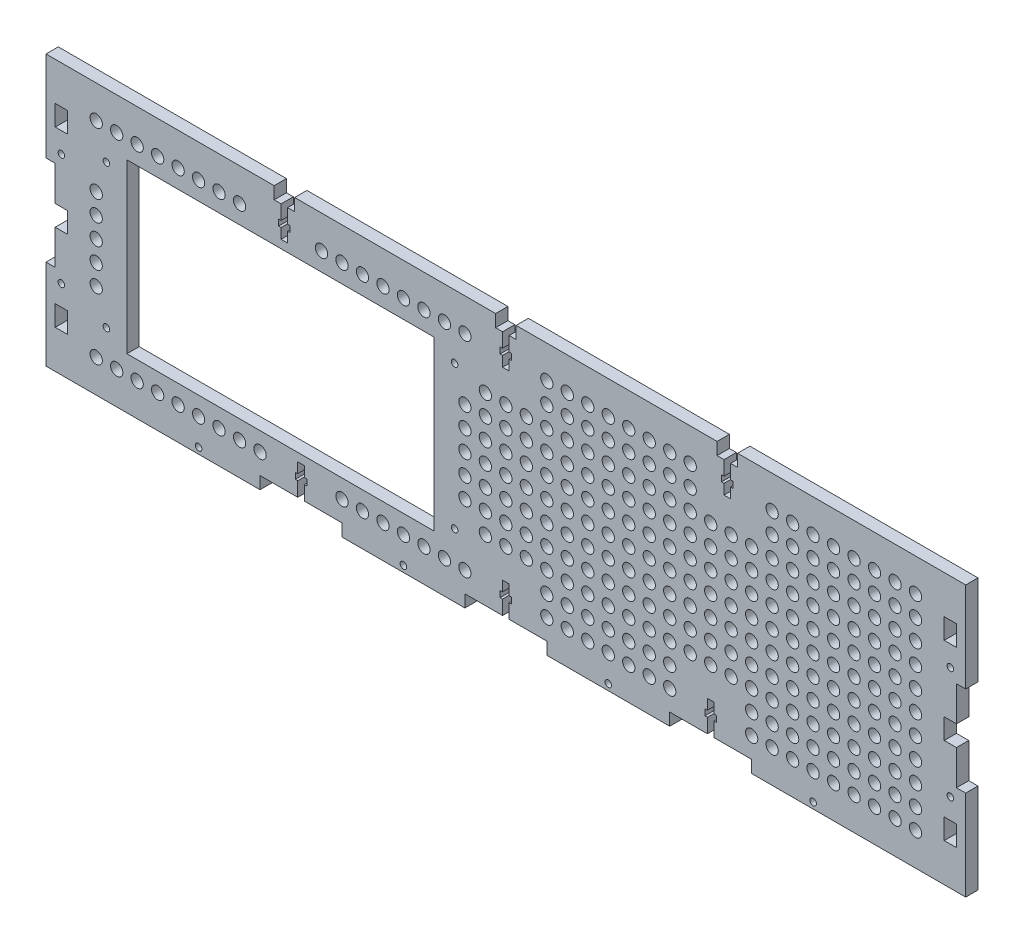
SolidWorks part; units mm, degrees
ref_plane "Front Plane" through (0, 0, 0) normal (0, 0, 1) x (1, 0, 0)
ref_plane "Top Plane" through (0, 0, 0) normal (0, 1, 0) x (1, 0, 0)
ref_plane "Right Plane" through (0, 0, 0) normal (1, 0, 0) x (0, 0, -1)
sketch "Sketch1" plane through (0, 0, 0) normal (0, 0, 1) x (1, 0, 0)
  line L1 (-220, -66) -> (220, -66)
  line L2 (-220, -66) -> (-220, 66)
  line L3 (-220, 66) -> (220, 66)
  line L4 (220, -66) -> (220, 66)
  line L5 (-220, -66) -> (220, 66) construction
  line L6 (-220, 66) -> (220, -66) construction
  point P0 (0, 0)
  dimension "D1" = 440
  dimension "D2" = 132
extrude "Boss-Extrude1" add sketch "Sketch1" along normal blind 6
sketch "Sketch2" plane through (0, 0, 0) normal (0, 0, -1) x (-1, 0, 0)
  line L0 (220, 47.3321) -> (220, 37.3321) construction
  line L1 (220, 37.3321) -> (214, 37.3321) construction
  line L2 (214, 37.3321) -> (214, 47.3321) construction
  line L3 (214, 47.3321) -> (220, 47.3321) construction
  line L12 (220, -37.3321) -> (220, -47.3321) construction
  line L13 (220, -47.3321) -> (214, -47.3321) construction
  line L14 (214, -47.3321) -> (214, -37.3321) construction
  line L15 (214, -37.3321) -> (220, -37.3321) construction
  line L16 (220, 47.3321) -> (220, 37.3321)
  line L17 (220, 37.3321) -> (214, 37.3321)
  line L18 (214, 37.3321) -> (214, 47.3321)
  line L19 (214, 47.3321) -> (220, 47.3321)
  line L20 (220, -37.3321) -> (220, -47.3321)
  line L21 (220, -47.3321) -> (214, -47.3321)
  line L22 (214, -47.3321) -> (214, -37.3321)
  line L23 (214, -37.3321) -> (220, -37.3321)
  line L24 (-214, -37.3321) -> (-214, -47.3321) construction
  line L25 (-214, -47.3321) -> (-220, -47.3321) construction
  line L26 (-220, -47.3321) -> (-220, -37.3321) construction
  line L27 (-220, -37.3321) -> (-214, -37.3321) construction
  line L28 (-214, 47.3321) -> (-214, 37.3321) construction
  line L29 (-214, 37.3321) -> (-220, 37.3321) construction
  line L30 (-220, 37.3321) -> (-220, 47.3321) construction
  line L31 (-220, 47.3321) -> (-214, 47.3321) construction
  line L32 (-214, -37.3321) -> (-214, -47.3321)
  line L33 (-214, -47.3321) -> (-220, -47.3321)
  line L34 (-220, -47.3321) -> (-220, -37.3321)
  line L35 (-220, -37.3321) -> (-214, -37.3321)
  line L36 (-214, 47.3321) -> (-214, 37.3321)
  line L37 (-214, 37.3321) -> (-220, 37.3321)
  line L38 (-220, 37.3321) -> (-220, 47.3321)
  line L39 (-220, 47.3321) -> (-214, 47.3321)
  line L44 (220, -5) -> (220, 5)
  line L45 (214, -5) -> (220, -5)
  line L46 (214, 5) -> (214, -5)
  line L47 (220, 5) -> (214, 5)
  line L48 (220, -5) -> (220, 5)
  line L49 (214, -5) -> (220, -5)
  line L50 (214, 5) -> (214, -5)
  line L51 (220, 5) -> (214, 5)
  line L52 (-214, -5) -> (-214, 5)
  line L53 (-220, -5) -> (-214, -5)
  line L54 (-220, 5) -> (-220, -5)
  line L55 (-214, 5) -> (-220, 5)
  line L56 (-214, -5) -> (-214, 5)
  line L57 (-220, -5) -> (-214, -5)
  line L58 (-220, 5) -> (-220, -5)
  line L59 (-214, 5) -> (-220, 5)
  circle A0 centre (217, 27.3321) radius 1.6 construction
  circle A1 centre (217, -27.3321) radius 1.6 construction
  circle A2 centre (-217, 27.3321) radius 1.6 construction
  circle A3 centre (-217, -27.3321) radius 1.6 construction
  circle A4 centre (217, 27.3321) radius 1.6
  circle A5 centre (217, -27.3321) radius 1.6
  circle A6 centre (-217, 27.3321) radius 1.6
  circle A7 centre (-217, -27.3321) radius 1.6
  dimension "D2" = 0
  dimension "D3" = 0
extrude "Cut-Extrude1" cut sketch "Sketch2" against normal up to next
sketch "Sketch3" plane through (0, 0, 0) normal (0, 0, -1) x (-1, 0, 0)
  circle A0 centre (-150, -63) radius 1.6 construction
  circle A1 centre (-50, -63) radius 1.6 construction
  circle A2 centre (50, -63) radius 1.6 construction
  circle A3 centre (150, -63) radius 1.6 construction
  circle A4 centre (-150, -63) radius 1.6
  circle A5 centre (-50, -63) radius 1.6
  circle A6 centre (50, -63) radius 1.6
  circle A7 centre (150, -63) radius 1.6
extrude "Cut-Extrude2" cut sketch "Sketch3" against normal up to next
sketch "Sketch4" plane through (0, 0, 0) normal (0, 0, -1) x (-1, 0, 0)
  line L0 (80, -66) -> (120, -66) construction
  line L1 (120, -66) -> (120, -60) construction
  line L2 (120, -60) -> (80, -60) construction
  line L3 (80, -60) -> (80, -66) construction
  line L4 (-20, -66) -> (20, -66) construction
  line L5 (20, -66) -> (20, -60) construction
  line L6 (20, -60) -> (-20, -60) construction
  line L7 (-20, -60) -> (-20, -66) construction
  line L8 (-120, -66) -> (-80, -66) construction
  line L9 (-80, -66) -> (-80, -60) construction
  line L10 (-80, -60) -> (-120, -60) construction
  line L11 (-120, -60) -> (-120, -66) construction
  line L12 (80, -66) -> (120, -66)
  line L13 (120, -66) -> (120, -60)
  line L14 (120, -60) -> (80, -60)
  line L15 (80, -60) -> (80, -66)
  line L16 (-20, -66) -> (20, -66)
  line L17 (20, -66) -> (20, -60)
  line L18 (20, -60) -> (-20, -60)
  line L19 (-20, -60) -> (-20, -66)
  line L20 (-120, -66) -> (-80, -66)
  line L21 (-80, -66) -> (-80, -60)
  line L22 (-80, -60) -> (-120, -60)
  line L23 (-120, -60) -> (-120, -66)
extrude "Cut-Extrude3" cut sketch "Sketch4" against normal up to next
sketch "Sketch5" plane through (0, 66, 0) normal (0, 1, 0) x (1, 0, 0)
  line L0 (220, 0) -> (-220, 0) construction
  line L1 (-113.125, -6) -> (-103.125, -6)
  line L2 (-113.125, -6) -> (-113.125, 0)
  line L3 (-113.125, 0) -> (-103.125, 0)
  line L4 (-103.125, -6) -> (-103.125, 0)
  line L5 (-113.125, -6) -> (-103.125, 0) construction
  line L6 (-113.125, 0) -> (-103.125, -6) construction
  line L7 (-103.125, -6) -> (-103.125, 0) construction
  line L8 (5, -6) -> (5, 0) construction
  line L9 (-5, -6) -> (5, -6)
  line L10 (-5, -6) -> (-5, 0)
  line L11 (-5, 0) -> (5, 0)
  line L12 (5, -6) -> (5, 0)
  line L13 (-5, -6) -> (5, 0) construction
  line L14 (-5, 0) -> (5, -6) construction
  line L15 (113.125, -6) -> (113.125, 0) construction
  line L16 (103.125, -6) -> (113.125, -6)
  line L17 (103.125, -6) -> (103.125, 0)
  line L18 (103.125, 0) -> (113.125, 0)
  line L19 (113.125, -6) -> (113.125, 0)
  line L20 (103.125, -6) -> (113.125, 0) construction
  line L21 (103.125, 0) -> (113.125, -6) construction
  point P0 (-108.125, -3)
  point P10 (0, -3)
  point P18 (108.125, -3)
extrude "Cut-Extrude4" cut sketch "Sketch5" against normal blind 6
sketch "Sketch6" plane through (0, 0, 0) normal (0, 0, -1) x (-1, 0, 0)
  line L0 (-108.125, 60) -> (-108.125, 45) construction
  line L1 (-113.125, 60) -> (-103.125, 60) construction
  line L2 (-109.725, 60) -> (-109.725, 53)
  line L3 (-106.525, 60) -> (-106.525, 53)
  line L4 (-109.725, 60) -> (-106.525, 60)
  line L5 (-109.725, 45) -> (-106.525, 45)
  line L6 (-106.525, 50) -> (-105.325, 50)
  line L7 (-110.925, 53) -> (-109.725, 53)
  line L8 (-110.925, 53) -> (-110.925, 50)
  line L9 (-110.925, 50) -> (-109.725, 50)
  line L10 (-105.325, 53) -> (-105.325, 50)
  line L11 (-110.925, 53) -> (-105.325, 50) construction
  line L12 (-110.925, 50) -> (-105.325, 53) construction
  line L13 (-106.525, 50) -> (-106.525, 45)
  line L14 (-106.525, 60) -> (-106.525, 45) construction
  line L15 (-109.725, 50) -> (-109.725, 45)
  line L16 (-109.725, 60) -> (-109.725, 45) construction
  line L17 (-106.525, 53) -> (-105.325, 53)
  line L18 (-1.595, 60) -> (-1.595, 53)
  line L19 (1.605, 60) -> (1.605, 53)
  line L20 (-1.595, 60) -> (1.605, 60)
  line L21 (-1.595, 45) -> (1.605, 45)
  line L22 (1.605, 50) -> (2.805, 50)
  line L23 (-2.795, 53) -> (-1.595, 53)
  line L24 (-2.795, 53) -> (-2.795, 50)
  line L25 (-2.795, 50) -> (-1.595, 50)
  line L26 (2.805, 53) -> (2.805, 50)
  line L27 (1.605, 50) -> (1.605, 45)
  line L28 (-1.595, 50) -> (-1.595, 45)
  line L29 (1.605, 53) -> (2.805, 53)
  line L30 (0.005, 60) -> (0.005, 45) construction
  line L31 (-2.795, 53) -> (2.805, 50) construction
  line L32 (-2.795, 50) -> (2.805, 53) construction
  line L33 (106.535, 60) -> (106.535, 53)
  line L34 (109.735, 60) -> (109.735, 53)
  line L35 (106.535, 60) -> (109.735, 60)
  line L36 (106.535, 45) -> (109.735, 45)
  line L37 (109.735, 50) -> (110.935, 50)
  line L38 (105.335, 53) -> (106.535, 53)
  line L39 (105.335, 53) -> (105.335, 50)
  line L40 (105.335, 50) -> (106.535, 50)
  line L41 (110.935, 53) -> (110.935, 50)
  line L42 (109.735, 50) -> (109.735, 45)
  line L43 (106.535, 50) -> (106.535, 45)
  line L44 (109.735, 53) -> (110.935, 53)
  line L45 (108.135, 60) -> (108.135, 45) construction
  line L46 (105.335, 53) -> (110.935, 50) construction
  line L47 (105.335, 50) -> (110.935, 53) construction
  line L48 (-100, -60) -> (-100, -45) construction
  line L49 (-80, -60) -> (-120, -60) construction
  line L50 (-98.4, -60) -> (-98.4, -53)
  line L51 (-101.6, -60) -> (-101.6, -53)
  line L52 (-98.4, -60) -> (-101.6, -60)
  line L53 (-98.4, -45) -> (-101.6, -45)
  line L54 (-98.4, -53) -> (-97.2, -53)
  line L55 (-102.8, -50) -> (-101.6, -50)
  line L56 (-102.8, -50) -> (-102.8, -53)
  line L57 (-102.8, -53) -> (-101.6, -53)
  line L58 (-97.2, -50) -> (-97.2, -53)
  line L59 (-102.8, -50) -> (-97.2, -53) construction
  line L60 (-102.8, -53) -> (-97.2, -50) construction
  line L61 (-98.4, -50) -> (-98.4, -45)
  line L62 (-98.4, -60) -> (-98.4, -45) construction
  line L63 (-98.4, -50) -> (-97.2, -50)
  line L64 (-101.6, -50) -> (-101.6, -45)
  line L65 (-101.6, -60) -> (-101.6, -45) construction
  line L66 (1.6, -60) -> (1.6, -53)
  line L67 (1.6, -60) -> (-1.6, -60)
  line L68 (-1.6, -60) -> (-1.6, -53)
  line L69 (-2.8, -53) -> (-1.6, -53)
  line L70 (-2.8, -50) -> (-2.8, -53)
  line L71 (-2.8, -50) -> (-1.6, -50)
  line L72 (-1.6, -50) -> (-1.6, -45)
  line L73 (1.6, -45) -> (-1.6, -45)
  line L74 (1.6, -50) -> (1.6, -45)
  line L75 (1.6, -50) -> (2.8, -50)
  line L76 (2.8, -50) -> (2.8, -53)
  line L77 (1.6, -53) -> (2.8, -53)
  line L78 (101.6, -60) -> (101.6, -53)
  line L79 (101.6, -60) -> (98.4, -60)
  line L80 (98.4, -60) -> (98.4, -53)
  line L81 (97.2, -53) -> (98.4, -53)
  line L82 (97.2, -50) -> (97.2, -53)
  line L83 (97.2, -50) -> (98.4, -50)
  line L84 (98.4, -50) -> (98.4, -45)
  line L85 (101.6, -45) -> (98.4, -45)
  line L86 (101.6, -50) -> (101.6, -45)
  line L87 (101.6, -50) -> (102.8, -50)
  line L88 (102.8, -50) -> (102.8, -53)
  line L89 (101.6, -53) -> (102.8, -53)
  point P8 (-108.125, 51.5)
  point P25 (0.005, 51.5)
  point P40 (108.135, 51.5)
  point P55 (-100, -51.5)
  dimension "D1" = 15
  dimension "D4" = 5.6
  dimension "D5" = 3
  dimension "D6" = 7
  dimension "D8" = 15
  dimension "D11" = 7
  dimension "D12" = 3
  dimension "D13" = 5.6
  dimension "D2" = 1.6
  dimension "D3" = 1.6
  dimension "D9" = 1.6
  dimension "D10" = 1.6
  dimension "D7" = 3
  dimension "D14" = 3
extrude "Cut-Extrude5" cut sketch "Sketch6" against normal up to next
sketch "Sketch7" plane through (0, 0, 0) normal (0, 0, -1) x (-1, 0, 0)
  line L0 (0, 0) -> (220, 0) construction
  line L1 (220, 37.3321) -> (220, 5) construction
  line L2 (113.125, 66) -> (220, 66) construction
  line L3 (35, -41) -> (185, -41)
  line L4 (35, -41) -> (35, 41)
  line L5 (35, 41) -> (185, 41)
  line L6 (185, -41) -> (185, 41)
  line L7 (35, -41) -> (185, 41) construction
  line L8 (35, 41) -> (185, -41) construction
  line L9 (25, 35) -> (25, -35) construction
  line L10 (25, 35) -> (195, 35) construction
  line L11 (25, -35) -> (35, -35) construction
  line L12 (195, -35) -> (185, -35) construction
  circle A0 centre (25, 35) radius 1.6
  circle A1 centre (25, -35) radius 1.6
  circle A2 centre (195, 35) radius 1.6
  circle A3 centre (195, -35) radius 1.6
  point P3 (110, 0)
  point P4 (110, 0)
  point P21 (110, 35)
  point P22 (25, 0)
  dimension "D5" = 3.2
  dimension "D1" = 25
  dimension "D2" = 150
  dimension "D3" = 10
  dimension "D4" = 70
extrude "Cut-Extrude6" cut sketch "Sketch7" against normal through all
sketch "Sketch8" plane through (0, 0, 0) normal (0, 0, -1) x (-1, 0, 0)
  line L10 (-200, 50) -> (-220, 50) construction
  line L13 (-220, 22) -> (-220, 66) construction
  line L16 (200, 50) -> (220, 50) construction
  line L19 (220, 22) -> (220, 66) construction
  line L22 (-200, 50) -> (-200, 66) construction
  line L25 (-220, 66) -> (-113.125, 66) construction
  line L28 (-200, -50) -> (-200, -66) construction
  line L31 (-120, -66) -> (-220, -66) construction
  circle A128 centre (-200, 50) radius 3
  circle A129 centre (-190, 50) radius 3
  circle A130 centre (-180, 50) radius 3
  circle A131 centre (-170, 50) radius 3
  circle A132 centre (-160, 50) radius 3
  circle A133 centre (-150, 50) radius 3
  circle A134 centre (-140, 50) radius 3
  circle A135 centre (-130, 50) radius 3
  circle A139 centre (-90, 50) radius 3
  circle A140 centre (-80, 50) radius 3
  circle A141 centre (-70, 50) radius 3
  circle A142 centre (-60, 50) radius 3
  circle A143 centre (-50, 50) radius 3
  circle A144 centre (-40, 50) radius 3
  circle A145 centre (-30, 50) radius 3
  circle A146 centre (-20, 50) radius 3
  circle A150 centre (20, 50) radius 3
  circle A151 centre (30, 50) radius 3
  circle A152 centre (40, 50) radius 3
  circle A153 centre (50, 50) radius 3
  circle A154 centre (60, 50) radius 3
  circle A155 centre (70, 50) radius 3
  circle A156 centre (80, 50) radius 3
  circle A157 centre (90, 50) radius 3
  circle A161 centre (130, 50) radius 3
  circle A162 centre (140, 50) radius 3
  circle A163 centre (150, 50) radius 3
  circle A164 centre (160, 50) radius 3
  circle A165 centre (170, 50) radius 3
  circle A166 centre (180, 50) radius 3
  circle A167 centre (190, 50) radius 3
  circle A168 centre (200, 50) radius 3
  circle A169 centre (-190, 40) radius 3
  circle A170 centre (-180, 40) radius 3
  circle A171 centre (-170, 40) radius 3
  circle A172 centre (-160, 40) radius 3
  circle A173 centre (-150, 40) radius 3
  circle A174 centre (-140, 40) radius 3
  circle A175 centre (-130, 40) radius 3
  circle A179 centre (-90, 40) radius 3
  circle A180 centre (-80, 40) radius 3
  circle A181 centre (-70, 40) radius 3
  circle A182 centre (-60, 40) radius 3
  circle A183 centre (-50, 40) radius 3
  circle A184 centre (-40, 40) radius 3
  circle A185 centre (-30, 40) radius 3
  circle A186 centre (-20, 40) radius 3
  circle A209 centre (-190, 30) radius 3
  circle A210 centre (-180, 30) radius 3
  circle A211 centre (-170, 30) radius 3
  circle A212 centre (-160, 30) radius 3
  circle A213 centre (-150, 30) radius 3
  circle A214 centre (-140, 30) radius 3
  circle A215 centre (-130, 30) radius 3
  circle A216 centre (-120, 30) radius 3
  circle A217 centre (-110, 30) radius 3
  circle A218 centre (-100, 30) radius 3
  circle A219 centre (-90, 30) radius 3
  circle A220 centre (-80, 30) radius 3
  circle A221 centre (-70, 30) radius 3
  circle A222 centre (-60, 30) radius 3
  circle A223 centre (-50, 30) radius 3
  circle A224 centre (-40, 30) radius 3
  circle A225 centre (-30, 30) radius 3
  circle A226 centre (-20, 30) radius 3
  circle A227 centre (-10, 30) radius 3
  circle A228 centre (0, 30) radius 3
  circle A229 centre (10, 30) radius 3
  circle A249 centre (-190, 20) radius 3
  circle A250 centre (-180, 20) radius 3
  circle A251 centre (-170, 20) radius 3
  circle A252 centre (-160, 20) radius 3
  circle A253 centre (-150, 20) radius 3
  circle A254 centre (-140, 20) radius 3
  circle A255 centre (-130, 20) radius 3
  circle A256 centre (-120, 20) radius 3
  circle A257 centre (-110, 20) radius 3
  circle A258 centre (-100, 20) radius 3
  circle A259 centre (-90, 20) radius 3
  circle A260 centre (-80, 20) radius 3
  circle A261 centre (-70, 20) radius 3
  circle A262 centre (-60, 20) radius 3
  circle A263 centre (-50, 20) radius 3
  circle A264 centre (-40, 20) radius 3
  circle A265 centre (-30, 20) radius 3
  circle A266 centre (-20, 20) radius 3
  circle A267 centre (-10, 20) radius 3
  circle A268 centre (0, 20) radius 3
  circle A269 centre (10, 20) radius 3
  circle A270 centre (20, 20) radius 3
  circle A288 centre (200, 20) radius 3
  circle A289 centre (-190, 10) radius 3
  circle A290 centre (-180, 10) radius 3
  circle A291 centre (-170, 10) radius 3
  circle A292 centre (-160, 10) radius 3
  circle A293 centre (-150, 10) radius 3
  circle A294 centre (-140, 10) radius 3
  circle A295 centre (-130, 10) radius 3
  circle A296 centre (-120, 10) radius 3
  circle A297 centre (-110, 10) radius 3
  circle A298 centre (-100, 10) radius 3
  circle A299 centre (-90, 10) radius 3
  circle A300 centre (-80, 10) radius 3
  circle A301 centre (-70, 10) radius 3
  circle A302 centre (-60, 10) radius 3
  circle A303 centre (-50, 10) radius 3
  circle A304 centre (-40, 10) radius 3
  circle A305 centre (-30, 10) radius 3
  circle A306 centre (-20, 10) radius 3
  circle A307 centre (-10, 10) radius 3
  circle A308 centre (0, 10) radius 3
  circle A309 centre (10, 10) radius 3
  circle A310 centre (20, 10) radius 3
  circle A328 centre (200, 10) radius 3
  circle A329 centre (-190, 0) radius 3
  circle A330 centre (-180, 0) radius 3
  circle A331 centre (-170, 0) radius 3
  circle A332 centre (-160, 0) radius 3
  circle A333 centre (-150, 0) radius 3
  circle A334 centre (-140, 0) radius 3
  circle A335 centre (-130, 0) radius 3
  circle A336 centre (-120, 0) radius 3
  circle A337 centre (-110, 0) radius 3
  circle A338 centre (-100, 0) radius 3
  circle A339 centre (-90, 0) radius 3
  circle A340 centre (-80, 0) radius 3
  circle A341 centre (-70, 0) radius 3
  circle A342 centre (-60, 0) radius 3
  circle A343 centre (-50, 0) radius 3
  circle A344 centre (-40, 0) radius 3
  circle A345 centre (-30, 0) radius 3
  circle A346 centre (-20, 0) radius 3
  circle A347 centre (-10, 0) radius 3
  circle A348 centre (0, 0) radius 3
  circle A349 centre (10, 0) radius 3
  circle A350 centre (20, 0) radius 3
  circle A368 centre (200, 0) radius 3
  circle A369 centre (-190, -10) radius 3
  circle A370 centre (-180, -10) radius 3
  circle A371 centre (-170, -10) radius 3
  circle A372 centre (-160, -10) radius 3
  circle A373 centre (-150, -10) radius 3
  circle A374 centre (-140, -10) radius 3
  circle A375 centre (-130, -10) radius 3
  circle A376 centre (-120, -10) radius 3
  circle A377 centre (-110, -10) radius 3
  circle A378 centre (-100, -10) radius 3
  circle A379 centre (-90, -10) radius 3
  circle A380 centre (-80, -10) radius 3
  circle A381 centre (-70, -10) radius 3
  circle A382 centre (-60, -10) radius 3
  circle A383 centre (-50, -10) radius 3
  circle A384 centre (-40, -10) radius 3
  circle A385 centre (-30, -10) radius 3
  circle A386 centre (-20, -10) radius 3
  circle A387 centre (-10, -10) radius 3
  circle A388 centre (0, -10) radius 3
  circle A389 centre (10, -10) radius 3
  circle A390 centre (20, -10) radius 3
  circle A408 centre (200, -10) radius 3
  circle A409 centre (-190, -20) radius 3
  circle A410 centre (-180, -20) radius 3
  circle A411 centre (-170, -20) radius 3
  circle A412 centre (-160, -20) radius 3
  circle A413 centre (-150, -20) radius 3
  circle A414 centre (-140, -20) radius 3
  circle A415 centre (-130, -20) radius 3
  circle A416 centre (-120, -20) radius 3
  circle A417 centre (-110, -20) radius 3
  circle A418 centre (-100, -20) radius 3
  circle A419 centre (-90, -20) radius 3
  circle A420 centre (-80, -20) radius 3
  circle A421 centre (-70, -20) radius 3
  circle A422 centre (-60, -20) radius 3
  circle A423 centre (-50, -20) radius 3
  circle A424 centre (-40, -20) radius 3
  circle A425 centre (-30, -20) radius 3
  circle A426 centre (-20, -20) radius 3
  circle A427 centre (-10, -20) radius 3
  circle A428 centre (0, -20) radius 3
  circle A429 centre (10, -20) radius 3
  circle A430 centre (20, -20) radius 3
  circle A448 centre (200, -20) radius 3
  circle A449 centre (-190, -30) radius 3
  circle A450 centre (-180, -30) radius 3
  circle A451 centre (-170, -30) radius 3
  circle A452 centre (-160, -30) radius 3
  circle A453 centre (-150, -30) radius 3
  circle A454 centre (-140, -30) radius 3
  circle A455 centre (-130, -30) radius 3
  circle A456 centre (-120, -30) radius 3
  circle A457 centre (-110, -30) radius 3
  circle A458 centre (-100, -30) radius 3
  circle A459 centre (-90, -30) radius 3
  circle A460 centre (-80, -30) radius 3
  circle A461 centre (-70, -30) radius 3
  circle A462 centre (-60, -30) radius 3
  circle A463 centre (-50, -30) radius 3
  circle A464 centre (-40, -30) radius 3
  circle A465 centre (-30, -30) radius 3
  circle A466 centre (-20, -30) radius 3
  circle A467 centre (-10, -30) radius 3
  circle A468 centre (0, -30) radius 3
  circle A469 centre (10, -30) radius 3
  circle A489 centre (-190, -40) radius 3
  circle A490 centre (-180, -40) radius 3
  circle A491 centre (-170, -40) radius 3
  circle A492 centre (-160, -40) radius 3
  circle A493 centre (-150, -40) radius 3
  circle A494 centre (-140, -40) radius 3
  circle A495 centre (-130, -40) radius 3
  circle A496 centre (-120, -40) radius 3
  circle A500 centre (-80, -40) radius 3
  circle A501 centre (-70, -40) radius 3
  circle A502 centre (-60, -40) radius 3
  circle A503 centre (-50, -40) radius 3
  circle A504 centre (-40, -40) radius 3
  circle A505 centre (-30, -40) radius 3
  circle A506 centre (-20, -40) radius 3
  circle A529 centre (-190, -50) radius 3
  circle A530 centre (-180, -50) radius 3
  circle A531 centre (-170, -50) radius 3
  circle A532 centre (-160, -50) radius 3
  circle A533 centre (-150, -50) radius 3
  circle A534 centre (-140, -50) radius 3
  circle A535 centre (-130, -50) radius 3
  circle A536 centre (-120, -50) radius 3
  circle A540 centre (-80, -50) radius 3
  circle A541 centre (-70, -50) radius 3
  circle A542 centre (-60, -50) radius 3
  circle A543 centre (-50, -50) radius 3
  circle A544 centre (-40, -50) radius 3
  circle A545 centre (-30, -50) radius 3
  circle A546 centre (-20, -50) radius 3
  circle A550 centre (20, -50) radius 3
  circle A551 centre (30, -50) radius 3
  circle A552 centre (40, -50) radius 3
  circle A553 centre (50, -50) radius 3
  circle A554 centre (60, -50) radius 3
  circle A555 centre (70, -50) radius 3
  circle A556 centre (80, -50) radius 3
  circle A560 centre (120, -50) radius 3
  circle A561 centre (130, -50) radius 3
  circle A562 centre (140, -50) radius 3
  circle A563 centre (150, -50) radius 3
  circle A564 centre (160, -50) radius 3
  circle A565 centre (170, -50) radius 3
  circle A566 centre (180, -50) radius 3
  circle A567 centre (190, -50) radius 3
  circle A568 centre (200, -50) radius 3
  circle A569 centre (-200, 40) radius 3
  circle A570 centre (-200, 30) radius 3
  circle A571 centre (-200, 20) radius 3
  circle A572 centre (-200, 10) radius 3
  circle A573 centre (-200, 0) radius 3
  circle A574 centre (-200, -10) radius 3
  circle A575 centre (-200, -20) radius 3
  circle A576 centre (-200, -30) radius 3
  circle A577 centre (-200, -40) radius 3
  circle A578 centre (-200, -50) radius 3
  circle A579 centre (-110, 50) radius 3 [skipped]
  circle A580 centre (0, 50) radius 3 [skipped]
  circle A581 centre (110, 50) radius 3 [skipped]
  circle A582 centre (30, 40) radius 3 [skipped]
  circle A583 centre (40, 40) radius 3 [skipped]
  circle A584 centre (50, 40) radius 3 [skipped]
  circle A585 centre (60, 40) radius 3 [skipped]
  circle A586 centre (70, 40) radius 3 [skipped]
  circle A587 centre (80, 40) radius 3 [skipped]
  circle A588 centre (90, 40) radius 3 [skipped]
  circle A589 centre (100, 40) radius 3 [skipped]
  circle A590 centre (110, 40) radius 3 [skipped]
  circle A591 centre (120, 40) radius 3 [skipped]
  circle A592 centre (130, 40) radius 3 [skipped]
  circle A593 centre (140, 40) radius 3 [skipped]
  circle A594 centre (150, 40) radius 3 [skipped]
  circle A595 centre (160, 40) radius 3 [skipped]
  circle A596 centre (170, 40) radius 3 [skipped]
  circle A597 centre (180, 40) radius 3 [skipped]
  circle A598 centre (190, 40) radius 3 [skipped]
  circle A599 centre (30, 30) radius 3 [skipped]
  circle A600 centre (40, 30) radius 3 [skipped]
  circle A601 centre (50, 30) radius 3 [skipped]
  circle A602 centre (60, 30) radius 3 [skipped]
  circle A603 centre (70, 30) radius 3 [skipped]
  circle A604 centre (80, 30) radius 3 [skipped]
  circle A605 centre (90, 30) radius 3 [skipped]
  circle A606 centre (100, 30) radius 3 [skipped]
  circle A607 centre (110, 30) radius 3 [skipped]
  circle A608 centre (120, 30) radius 3 [skipped]
  circle A609 centre (130, 30) radius 3 [skipped]
  circle A610 centre (140, 30) radius 3 [skipped]
  circle A611 centre (150, 30) radius 3 [skipped]
  circle A612 centre (160, 30) radius 3 [skipped]
  circle A613 centre (170, 30) radius 3 [skipped]
  circle A614 centre (180, 30) radius 3 [skipped]
  circle A615 centre (190, 30) radius 3 [skipped]
  circle A616 centre (30, 20) radius 3 [skipped]
  circle A617 centre (40, 20) radius 3 [skipped]
  circle A618 centre (50, 20) radius 3 [skipped]
  circle A619 centre (60, 20) radius 3 [skipped]
  circle A620 centre (70, 20) radius 3 [skipped]
  circle A621 centre (80, 20) radius 3 [skipped]
  circle A622 centre (90, 20) radius 3 [skipped]
  circle A623 centre (100, 20) radius 3 [skipped]
  circle A624 centre (110, 20) radius 3 [skipped]
  circle A625 centre (120, 20) radius 3 [skipped]
  circle A626 centre (130, 20) radius 3 [skipped]
  circle A627 centre (140, 20) radius 3 [skipped]
  circle A628 centre (150, 20) radius 3 [skipped]
  circle A629 centre (160, 20) radius 3 [skipped]
  circle A630 centre (170, 20) radius 3 [skipped]
  circle A631 centre (180, 20) radius 3 [skipped]
  circle A632 centre (190, 20) radius 3 [skipped]
  circle A633 centre (30, 10) radius 3 [skipped]
  circle A634 centre (40, 10) radius 3 [skipped]
  circle A635 centre (50, 10) radius 3 [skipped]
  circle A636 centre (60, 10) radius 3 [skipped]
  circle A637 centre (70, 10) radius 3 [skipped]
  circle A638 centre (80, 10) radius 3 [skipped]
  circle A639 centre (90, 10) radius 3 [skipped]
  circle A640 centre (100, 10) radius 3 [skipped]
  circle A641 centre (110, 10) radius 3 [skipped]
  circle A642 centre (120, 10) radius 3 [skipped]
  circle A643 centre (130, 10) radius 3 [skipped]
  circle A644 centre (140, 10) radius 3 [skipped]
  circle A645 centre (150, 10) radius 3 [skipped]
  circle A646 centre (160, 10) radius 3 [skipped]
  circle A647 centre (170, 10) radius 3 [skipped]
  circle A648 centre (180, 10) radius 3 [skipped]
  circle A649 centre (190, 10) radius 3 [skipped]
  circle A650 centre (30, 0) radius 3 [skipped]
  circle A651 centre (40, 0) radius 3 [skipped]
  circle A652 centre (50, 0) radius 3 [skipped]
  circle A653 centre (60, 0) radius 3 [skipped]
  circle A654 centre (70, 0) radius 3 [skipped]
  circle A655 centre (80, 0) radius 3 [skipped]
  circle A656 centre (90, 0) radius 3 [skipped]
  circle A657 centre (100, 0) radius 3 [skipped]
  circle A658 centre (110, 0) radius 3 [skipped]
  circle A659 centre (120, 0) radius 3 [skipped]
  circle A660 centre (130, 0) radius 3 [skipped]
  circle A661 centre (140, 0) radius 3 [skipped]
  circle A662 centre (150, 0) radius 3 [skipped]
  circle A663 centre (160, 0) radius 3 [skipped]
  circle A664 centre (170, 0) radius 3 [skipped]
  circle A665 centre (180, 0) radius 3 [skipped]
  circle A666 centre (190, 0) radius 3 [skipped]
  circle A667 centre (30, -10) radius 3 [skipped]
  circle A668 centre (40, -10) radius 3 [skipped]
  circle A669 centre (50, -10) radius 3 [skipped]
  circle A670 centre (60, -10) radius 3 [skipped]
  circle A671 centre (70, -10) radius 3 [skipped]
  circle A672 centre (80, -10) radius 3 [skipped]
  circle A673 centre (90, -10) radius 3 [skipped]
  circle A674 centre (100, -10) radius 3 [skipped]
  circle A675 centre (110, -10) radius 3 [skipped]
  circle A676 centre (120, -10) radius 3 [skipped]
  circle A677 centre (130, -10) radius 3 [skipped]
  circle A678 centre (140, -10) radius 3 [skipped]
  circle A679 centre (150, -10) radius 3 [skipped]
  circle A680 centre (160, -10) radius 3 [skipped]
  circle A681 centre (170, -10) radius 3 [skipped]
  circle A682 centre (180, -10) radius 3 [skipped]
  circle A683 centre (190, -10) radius 3 [skipped]
  circle A684 centre (30, -20) radius 3 [skipped]
  circle A685 centre (40, -20) radius 3 [skipped]
  circle A686 centre (50, -20) radius 3 [skipped]
  circle A687 centre (60, -20) radius 3 [skipped]
  circle A688 centre (70, -20) radius 3 [skipped]
  circle A689 centre (80, -20) radius 3 [skipped]
  circle A690 centre (90, -20) radius 3 [skipped]
  circle A691 centre (100, -20) radius 3 [skipped]
  circle A692 centre (110, -20) radius 3 [skipped]
  circle A693 centre (120, -20) radius 3 [skipped]
  circle A694 centre (130, -20) radius 3 [skipped]
  circle A695 centre (140, -20) radius 3 [skipped]
  circle A696 centre (150, -20) radius 3 [skipped]
  circle A697 centre (160, -20) radius 3 [skipped]
  circle A698 centre (170, -20) radius 3 [skipped]
  circle A699 centre (180, -20) radius 3 [skipped]
  circle A700 centre (190, -20) radius 3 [skipped]
  circle A701 centre (30, -30) radius 3 [skipped]
  circle A702 centre (40, -30) radius 3 [skipped]
  circle A703 centre (50, -30) radius 3 [skipped]
  circle A704 centre (60, -30) radius 3 [skipped]
  circle A705 centre (70, -30) radius 3 [skipped]
  circle A706 centre (80, -30) radius 3 [skipped]
  circle A707 centre (90, -30) radius 3 [skipped]
  circle A708 centre (100, -30) radius 3 [skipped]
  circle A709 centre (110, -30) radius 3 [skipped]
  circle A710 centre (120, -30) radius 3 [skipped]
  circle A711 centre (130, -30) radius 3 [skipped]
  circle A712 centre (140, -30) radius 3 [skipped]
  circle A713 centre (150, -30) radius 3 [skipped]
  circle A714 centre (160, -30) radius 3 [skipped]
  circle A715 centre (170, -30) radius 3 [skipped]
  circle A716 centre (180, -30) radius 3 [skipped]
  circle A717 centre (190, -30) radius 3 [skipped]
  circle A718 centre (30, -40) radius 3 [skipped]
  circle A719 centre (40, -40) radius 3 [skipped]
  circle A720 centre (50, -40) radius 3 [skipped]
  circle A721 centre (60, -40) radius 3 [skipped]
  circle A722 centre (70, -40) radius 3 [skipped]
  circle A723 centre (80, -40) radius 3 [skipped]
  circle A724 centre (90, -40) radius 3 [skipped]
  circle A725 centre (100, -40) radius 3 [skipped]
  circle A726 centre (110, -40) radius 3 [skipped]
  circle A727 centre (120, -40) radius 3 [skipped]
  circle A728 centre (130, -40) radius 3 [skipped]
  circle A729 centre (140, -40) radius 3 [skipped]
  circle A730 centre (150, -40) radius 3 [skipped]
  circle A731 centre (160, -40) radius 3 [skipped]
  circle A732 centre (170, -40) radius 3 [skipped]
  circle A733 centre (180, -40) radius 3 [skipped]
  circle A734 centre (190, -40) radius 3 [skipped]
  circle A735 centre (20, -40) radius 3 [skipped]
  circle A736 centre (20, -30) radius 3 [skipped]
  circle A737 centre (20, 30) radius 3 [skipped]
  circle A738 centre (20, 40) radius 3 [skipped]
  circle A739 centre (200, 30) radius 3 [skipped]
  circle A740 centre (200, 40) radius 3 [skipped]
  circle A741 centre (100, -50) radius 3 [skipped]
  circle A742 centre (0, -50) radius 3 [skipped]
  circle A743 centre (-100, -50) radius 3 [skipped]
  circle A744 centre (-100, 50) radius 3 [skipped]
  circle A745 centre (100, 50) radius 3 [skipped]
  circle A746 centre (10, 50) radius 3 [skipped]
  circle A747 centre (-10, 50) radius 3 [skipped]
  circle A748 centre (-90, -50) radius 3 [skipped]
  circle A749 centre (-110, -50) radius 3 [skipped]
  circle A750 centre (-10, -50) radius 3 [skipped]
  circle A751 centre (10, -50) radius 3 [skipped]
  circle A752 centre (90, -50) radius 3 [skipped]
  circle A753 centre (110, -50) radius 3 [skipped]
  circle A754 centre (200, -40) radius 3 [skipped]
  circle A755 centre (200, -30) radius 3 [skipped]
  circle A756 centre (0, -40) radius 3 [skipped]
  circle A757 centre (-100, -40) radius 3 [skipped]
  circle A758 centre (-110, -40) radius 3 [skipped]
  circle A759 centre (-90, -40) radius 3 [skipped]
  circle A760 centre (-10, -40) radius 3 [skipped]
  circle A761 centre (10, -40) radius 3 [skipped]
  circle A762 centre (-10, 40) radius 3 [skipped]
  circle A763 centre (0, 40) radius 3 [skipped]
  circle A764 centre (10, 40) radius 3 [skipped]
  circle A765 centre (-110, 40) radius 3 [skipped]
  circle A766 centre (-100, 40) radius 3 [skipped]
  circle A767 centre (-120, 50) radius 3 [skipped]
  circle A768 centre (-120, 40) radius 3 [skipped]
  circle A769 centre (120, 50) radius 3 [skipped]
  dimension "D1" = 6
  dimension "D2" = 10
  dimension "D3" = 10
  dimension "D4" = 41
  dimension "D5" = 11
extrude "Cut-Extrude7" cut sketch "Sketch8" against normal through all
sketch "Sketch9" plane through (0, 0, 0) normal (0, 0, -1) x (-1, 0, 0)
  line L1 (220, 66) -> (224.5, 66)
  line L2 (220, 66) -> (220, 22)
  line L3 (220, 22) -> (224.5, 22)
  line L4 (224.5, 66) -> (224.5, 22)
  line L5 (220, -66) -> (224.5, -66)
  line L6 (220, -66) -> (220, -22)
  line L7 (220, -22) -> (224.5, -22)
  line L8 (224.5, -66) -> (224.5, -22)
  line L9 (-220, -66) -> (-224.5, -66)
  line L10 (-220, -66) -> (-220, -22)
  line L11 (-220, -22) -> (-224.5, -22)
  line L12 (-224.5, -66) -> (-224.5, -22)
  line L13 (-220, 66) -> (-224.5, 66)
  line L14 (-220, 66) -> (-220, 22)
  line L15 (-220, 22) -> (-224.5, 22)
  line L16 (-224.5, 66) -> (-224.5, 22)
extrude "Boss-Extrude2" add sketch "Sketch9" against normal blind 6
equation "\"m3_depth\"=15"
equation "\"D1@Sketch6\"=\"m3_depth\""
equation "\"m3_nut_width\"=5.6"
equation "\"D4@Sketch6\"=\"m3_nut_width\""
equation "\"m3_nut_thickness\"=3"
equation "\"D5@Sketch6\"=\"m3_nut_thickness\""
equation "\"m3_nut_depth\"=7"
equation "\"D6@Sketch6\"=\"m3_nut_depth\""
